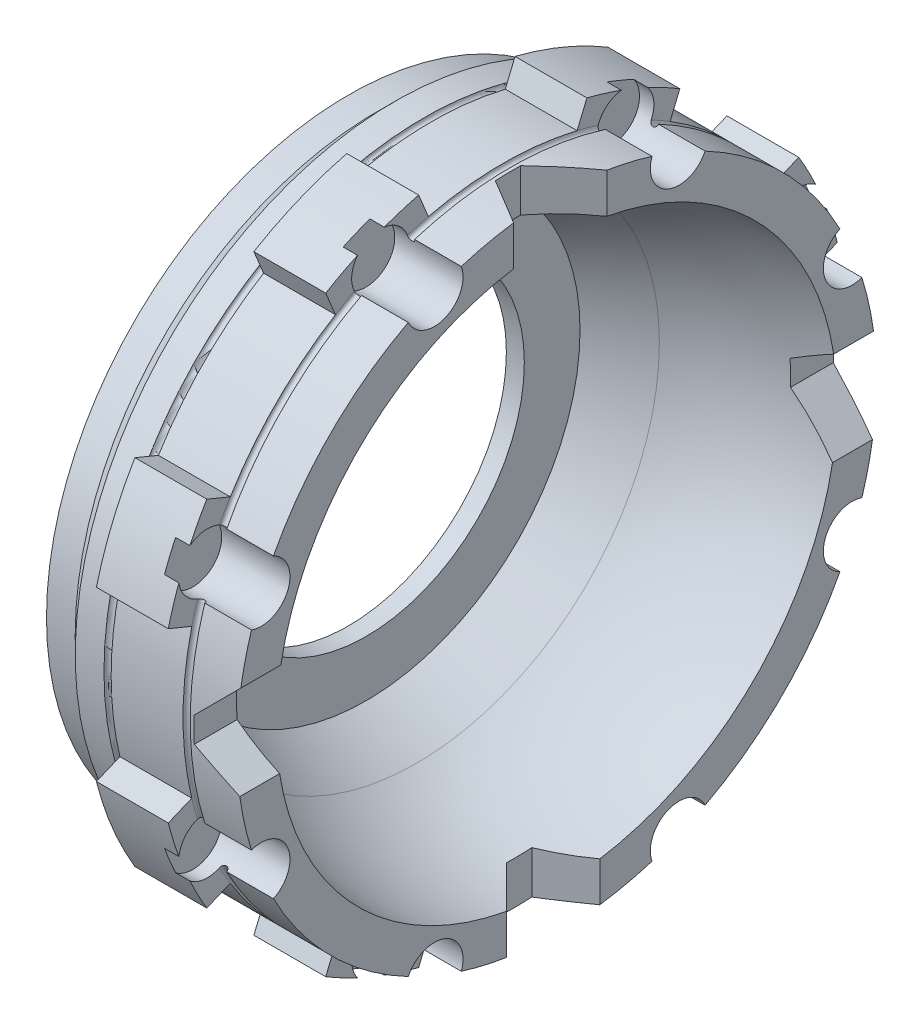
SolidWorks part; units mm, degrees
ref_plane "Přední rovina" through (0, 0, 0) normal (0, 0, 1) x (1, 0, 0)
ref_plane "Vrchní rovina" through (0, 0, 0) normal (0, 1, 0) x (1, 0, 0)
ref_plane "Pravá rovina" through (0, 0, 0) normal (1, 0, 0) x (0, 0, -1)
sketch "Skica1" plane through (0, 0, 0) normal (0, 0, 1) x (1, 0, 0)
  line L0 (0, 42) -> (4, 42)
  line L1 (4, 42) -> (6.5, 44.5)
  line L2 (6.5, 44.5) -> (29, 44.5)
  line L3 (29, 44.5) -> (29, 39.0165)
  line L4 (0, 22) -> (0, 42)
  line L5 (0, 22) -> (2.5, 22)
  line L6 (2.5, 22) -> (2.5, 29.75)
  line L7 (0, 0) -> (-52837.2145, 0) construction
  line L8 (0, 0) -> (0, 56.9694) construction
  line L9 (2.5, 29.75) -> (9.5, 33.7915)
  arc A1 (9.5, 33.7915) -> (29, 39.0165) centre (29, 0.0165) cw
  dimension "D9" = 39
  dimension "D1" = 84
  dimension "D2" = 89
  dimension "D3" = 2.5
  dimension "D4" = 4
  dimension "D5" = 29
  dimension "D6" = 44
  dimension "D7" = 59.5
  dimension "D8" = 30
  dimension "D10" = 7
  dimension "D11" = 26.5
revolve "Rotovat1" add sketch "Skica1" angle 360 about L7
sketch "Skica2" plane through (0, 0, 0) normal (0, 0, 1) x (1, 0, 0)
  line L0 (10.5, 44.5) -> (11.5, 44.5)
  line L1 (21.5, 44.5) -> (22.5, 44.5)
  line L2 (29, 44.5) -> (6.5, 44.5) construction
  line L3 (29, 44.5) -> (6.5, 44.5) construction
  line L4 (0, 42) -> (0, -42) construction
  line L5 (0, 0) -> (43.9834, 0) construction
  arc A0 (11.5, 44.5) -> (10.5, 44.5) centre (11, 44.5) cw
  arc A1 (22.5, 44.5) -> (21.5, 44.5) centre (22, 44.5) cw
  dimension "D1" = 0.5
  dimension "D2" = 0.5
  dimension "D3" = 11.5
  dimension "D4" = 10
revolve "Odebrat rotací1" cut sketch "Skica2" angle 360 about L5
ref_plane "Rovina1" through (21.5, 0, 0) normal (1, 0, 0) x (0, 0, -1)
ref_plane "Rovina2" through (11.5, 0, 0) normal (1, 0, 0) x (0, 0, -1)
sketch "Skica3" plane through (21.5, 0, 0) normal (1, 0, 0) x (0, 0, -1)
  line L0 (0, 0) -> (26.1983, 63.2483) construction
  line L3 (11.7053, 46.5509) -> (10.3502, 43.2796)
  line L5 (24.6396, 41.1933) -> (23.2846, 37.922)
  circle A0 centre (0, 0) radius 44.5 construction
  arc A1 (23.2846, 37.922) -> (10.3502, 43.2796) centre (0, 0) ccw
  arc A2 (24.6396, 41.1933) -> (11.7053, 46.5509) centre (0, 0) ccw
  point P2 (0, 70.1262)
  point P4 (0, 44.5)
  point P5 (6.8039, 47.1523)
  point P7 (-7, 47.4868)
  point P11 (28.374, 62.3027)
  dimension "D2" = 96
  dimension "D1" = 14
  dimension "D3" = 22.5
extrude "Přidat vysunutím1" add sketch "Skica3" against normal up to surface (10 mm away) up to plane "Rovina2"
sketch "Skica4" plane through (29, 0, 0) normal (1, 0, 0) x (0, 0, -1)
  line L0 (0, 58.5038) -> (0, 0) construction
  line L1 (0, 0) -> (17.0294, 41.1126) construction
  circle A0 centre (17.0294, 41.1126) radius 4
  circle A1 centre (0, 0) radius 44.5 construction
  circle A2 centre (0, 0) radius 44.5 construction
  point P8 (0, 0)
  point P9 (16.6929, 40.3002)
  dimension "D1" = 8
  dimension "D2" = 22.5
extrude "Odebrat vysunutím1" cut sketch "Skica4" against normal blind 9.5
pattern_circular "Kruhové pole1" count 8 over 360 about axis through (0, 0, 0) along (1, 0, 0) of "Přidat vysunutím1", "Odebrat vysunutím1"
ref_plane "Rovina3" through (0, 0, 44.5) normal (0, 0, 1) x (1, 0, 0)
sketch "Skica5" plane through (0, 0, 44.5) normal (0, 0, 1) x (1, 0, 0)
  line L0 (29, 7) -> (29, -6)
  line L1 (29, -6) -> (23, -2.5359)
  line L2 (23, -2.5359) -> (23, 1)
  line L3 (23, 1) -> (29, 7)
  line L4 (29, -39.4174) -> (29, -20.6524) construction
  line L5 (0, 0) -> (6.0562, 0) construction
  line L6 (0, 42) -> (0, -42) construction
  point P10 (23.964, 1.2492)
  dimension "D1" = 6
  dimension "D2" = 60
  dimension "D3" = 45
  dimension "D4" = 1
  dimension "D5" = 6
extrude "Odebrat vysunutím2" cut sketch "Skica5" against normal blind 9.5
pattern_circular "Kruhové pole2" count 4 over 360 about axis through (0, 0, 0) along (1, 0, 0) of "Odebrat vysunutím2"
